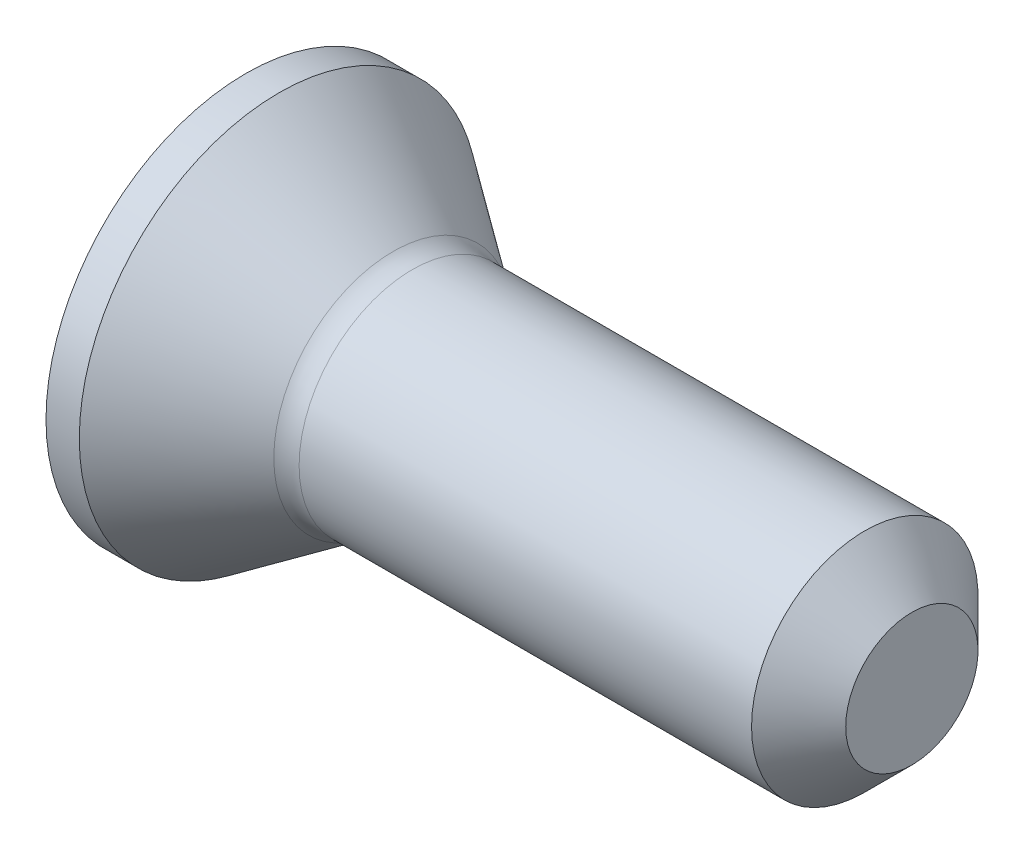
SolidWorks part; units mm, degrees
ref_plane "Front" through (0, 0, 0) normal (0, 0, 1) x (1, 0, 0)
ref_plane "Top" through (0, 0, 0) normal (0, 1, 0) x (1, 0, 0)
ref_plane "Right" through (0, 0, 0) normal (1, 0, 0) x (0, 0, -1)
sketch "Sketch1" plane through (0, 0, 0) normal (0, 0, 1) x (1, 0, 0)
  line L0 (0, 0) -> (0, 1.5)
  line L1 (0, 1.5) -> (0.25, 1.5)
  line L2 (0.25, 1.5) -> (1.1058, 0.8958)
  line L3 (1.25, 0.85) -> (4.6464, 0.85)
  line L6 (5, 0) -> (0, 0)
  line L7 (-3.9747, 0) -> (0, 0) construction
  line L9 (4.6464, 0.85) -> (5, 0.4964)
  line L10 (5, 0.4964) -> (5, 0)
  arc A0 (1.1058, 0.8958) -> (1.25, 0.85) centre (1.25, 1.1) ccw
  dimension "D3" = 0.25
  dimension "D1" = 135
  dimension "D2" = 1.7
  dimension "D4" = 1.25
  dimension "D5" = 0.25
  dimension "D6" = 0.5
  dimension "D7" = 5
  dimension "D9" = 3
revolve "Revolve1" add sketch "Sketch1" angle 360 about L7
sketch "Sketch2" plane through (0, 0, 0) normal (-1, 0, 0) x (0, 0, 1)
  line L0 (0.75, 0) -> (0, 0) construction
  line L1 (0, 0) -> (0, 0.75) construction
  line L2 (-0.175, 0.75) -> (0.175, 0.75)
  line L3 (0.175, 0.75) -> (0.2213, 0.2213)
  line L4 (0.2213, 0.2213) -> (0.75, 0.175)
  line L5 (0.75, 0.175) -> (0.75, -0.175)
  line L6 (-0.175, 0.75) -> (-0.2213, 0.2213)
  line L7 (-0.2213, 0.2213) -> (-0.75, 0.175)
  line L8 (-0.75, 0.175) -> (-0.75, -0.175)
  line L9 (-0.2213, -0.2213) -> (-0.75, -0.175)
  line L10 (-0.175, -0.75) -> (-0.2213, -0.2213)
  line L11 (-0.175, -0.75) -> (0.175, -0.75)
  line L12 (0.175, -0.75) -> (0.2213, -0.2213)
  line L13 (0.2213, -0.2213) -> (0.75, -0.175)
  point P12 (-0.75, 0)
  dimension "D1" = 95
  dimension "D2" = 1.5
  dimension "D3" = 0.35
extrude "Cut-Extrude1" cut sketch "Sketch2" against normal blind 0.5
